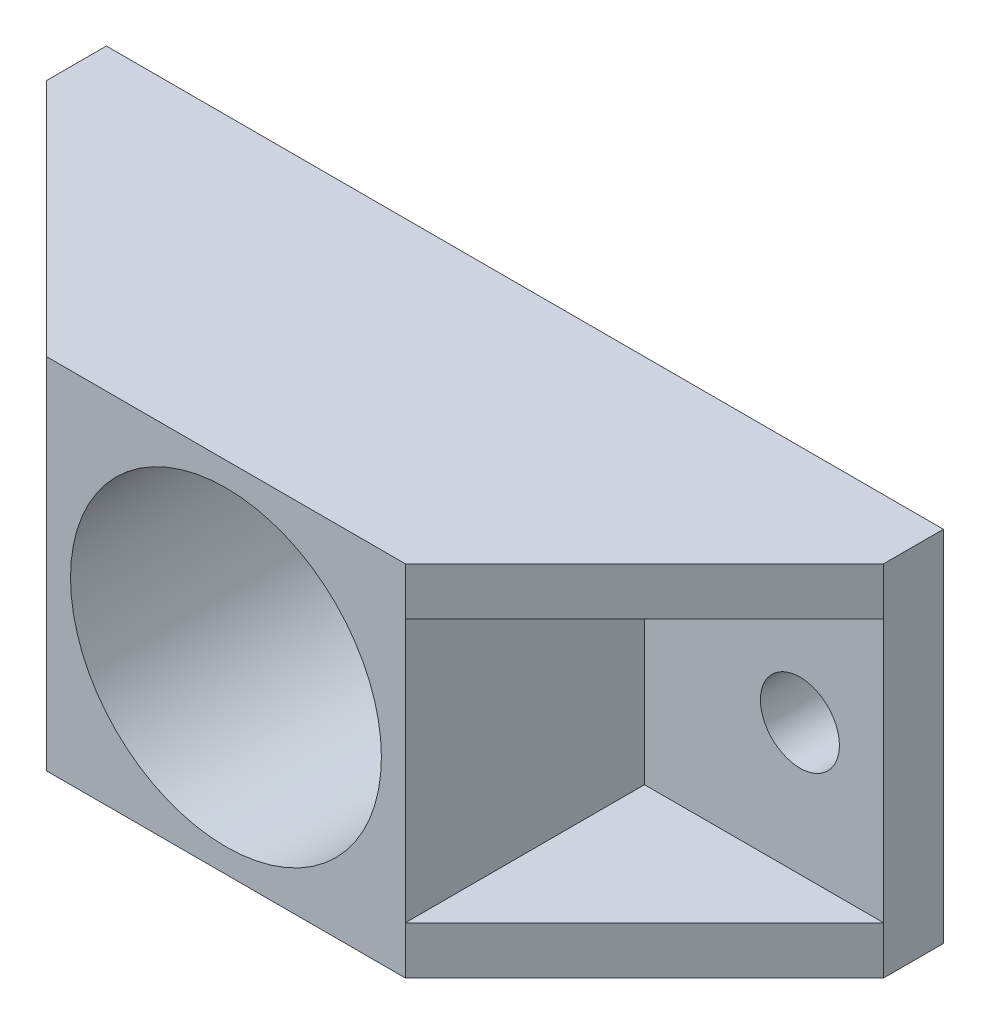
SolidWorks part; units mm, degrees
material "1.0503 (C45)"
ref_plane "前视基准面" through (0, 0, 0) normal (0, 0, 1) x (1, 0, 0)
ref_plane "上视基准面" through (0, 0, 0) normal (0, 1, 0) x (1, 0, 0)
ref_plane "右视基准面" through (0, 0, 0) normal (1, 0, 0) x (0, 0, -1)
sketch "草图1" plane through (0, 0, 0) normal (0, 0, 1) x (1, 0, 0)
  line L0 (-28, 0) -> (0, 0) construction
  line L1 (35, 15) -> (-35, 15)
  line L2 (35, 15) -> (35, -15)
  line L3 (35, -15) -> (-35, -15)
  line L4 (-35, 15) -> (-35, -15)
  line L5 (35, 15) -> (-35, -15) construction
  line L6 (35, -15) -> (-35, 15) construction
  line L7 (0, 0) -> (0, 15) construction
  circle A0 centre (-28, 0) radius 3.3
  circle A1 centre (28, 0) radius 3.3
  point P0 (0, 0)
  point P14 (-34.9878, 14.2589)
  point P17 (0, 0)
  dimension "D3" = 56
  dimension "D4" = 6.6
  dimension "D1" = 70
  dimension "D2" = 30
extrude "凸台-拉伸1" add sketch "草图1" along normal blind 5
sketch "草图2" plane through (0, 0, 5) normal (0, 0, 1) x (1, 0, 0)
  line L0 (35, 15) -> (-35, 15) construction
  line L1 (15, -15) -> (-15, -15)
  line L2 (15, -15) -> (15, 15)
  line L3 (15, 15) -> (-15, 15)
  line L4 (-15, -15) -> (-15, 15)
  line L5 (15, -15) -> (-15, 15) construction
  line L6 (15, 15) -> (-15, -15) construction
  point P0 (0, 0)
  dimension "D1" = 30
extrude "凸台-拉伸2" add sketch "草图2" along normal blind 20
sketch "草图3" plane through (0, 0, 25) normal (0, 0, 1) x (1, 0, 0)
  circle A0 centre (0, 0) radius 13
extrude "切除-拉伸1" cut sketch "草图3" against normal through all
sketch "草图5" plane through (0, -15, 0) normal (0, -1, 0) x (1, 0, 0)
  line L0 (-35, 5) -> (-15, 25)
  line L1 (-15, 25) -> (-15, 5)
  line L2 (-15, 5) -> (-35, 5)
  line L3 (15, 25) -> (35, 5)
  line L4 (35, 5) -> (15, 5)
  line L5 (15, 5) -> (15, 25)
extrude "凸台-拉伸3" add sketch "草图5" against normal blind 4
mirror "镜向1" about plane through (0, 0, 0) normal (0, 1, 0) of "凸台-拉伸3"
equation "\"6。5\"=6.16116"
